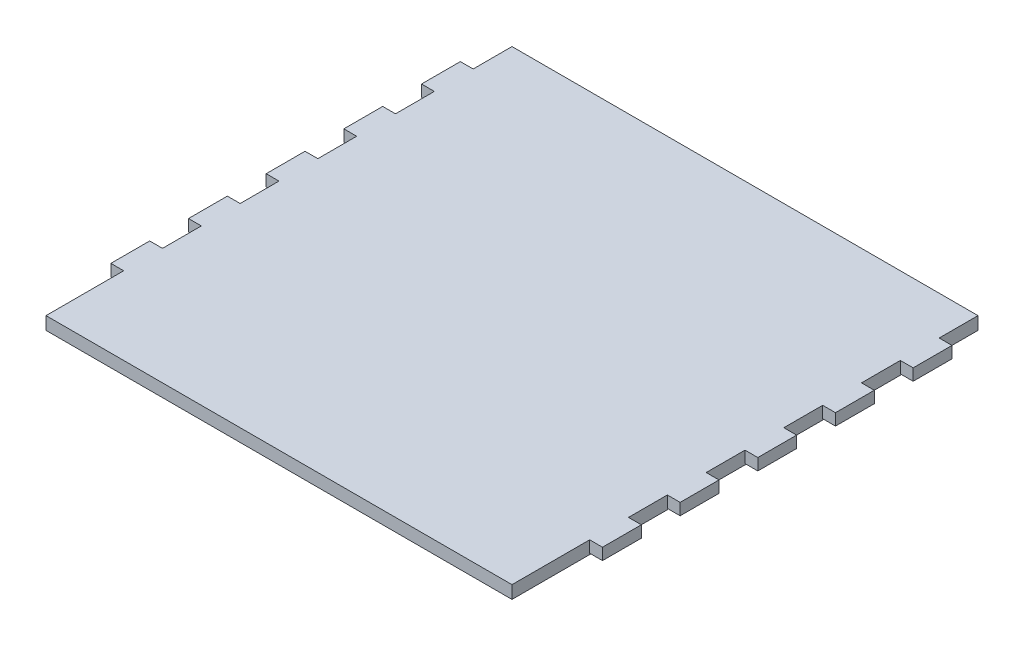
SolidWorks part; units mm, degrees
ref_plane "Front Plane" through (0, 0, 0) normal (0, 0, 1) x (1, 0, 0)
ref_plane "Top Plane" through (0, 0, 0) normal (0, 1, 0) x (1, 0, 0)
ref_plane "Right Plane" through (0, 0, 0) normal (1, 0, 0) x (0, 0, -1)
sketch "Sketch1" plane through (0, 0, 0) normal (0, 1, 0) x (1, 0, 0)
  line L1 (-60, 60) -> (60, 60)
  line L2 (-60, 60) -> (-60, -60)
  line L3 (-60, -60) -> (60, -60)
  line L4 (60, 60) -> (60, -60)
  line L5 (-60, 60) -> (60, -60) construction
  line L6 (-60, -60) -> (60, 60) construction
  point P0 (0, 0)
  dimension "D1" = 120
  dimension "D2" = 120
extrude "Boss-Extrude1" add sketch "Sketch1" along normal blind 3.3
sketch "Sketch2" plane through (0, 3.3, 0) normal (0, 1, 0) x (1, 0, 0)
  line L0 (60, -60) -> (60, 60) construction
  line L1 (60, 50) -> (63.3, 50)
  line L2 (60, 50) -> (60, 40)
  line L3 (60, 40) -> (63.3, 40)
  line L4 (63.3, 50) -> (63.3, 40)
  line L5 (60, 60) -> (-60, 60) construction
  dimension "D1" = 3.3
  dimension "D3" = 10
  dimension "D4" = 10
extrude "Boss-Extrude2" add sketch "Sketch2" against normal blind 3 contours L4 L3 L2 L1
pattern_linear "LPattern1" count 5 spacing 20 along (0, 0, 1) of "Boss-Extrude2"
mirror "Mirror1" about plane through (0, 0, 0) normal (1, 0, 0) of "LPattern1", "Boss-Extrude2"
